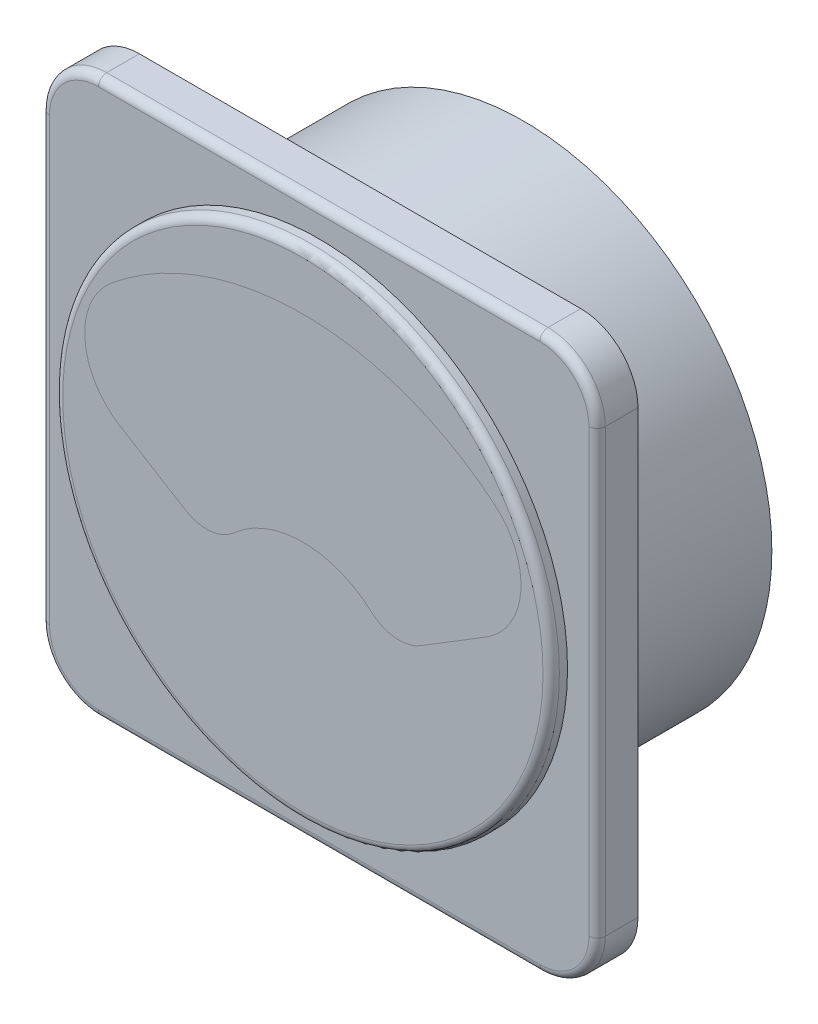
SolidWorks part; units mm, degrees
ref_plane "Front Plane" through (0, 0, 0) normal (0, 0, 1) x (1, 0, 0)
ref_plane "Top Plane" through (0, 0, 0) normal (0, 1, 0) x (1, 0, 0)
ref_plane "Right Plane" through (0, 0, 0) normal (1, 0, 0) x (0, 0, -1)
sketch "Sketch1" plane through (0, 0, 0) normal (0, 0, 1) x (1, 0, 0)
  circle A0 centre (0, 0) radius 30.3826
extrude "Boss-Extrude1" add sketch "Sketch1" against normal blind 20
sketch "Sketch2" plane through (0, 0, 0) normal (0, 0, 1) x (1, 0, 0)
  line L1 (-27, -34) -> (27, -34)
  line L2 (-34, -27) -> (-34, 27)
  line L3 (-27, 34) -> (27, 34)
  line L4 (34, -27) -> (34, 27)
  line L5 (-34, -34) -> (34, 34) construction
  line L6 (-34, 34) -> (34, -34) construction
  arc A0 (-34, 27) -> (-27, 34) centre (-27, 27) cw
  circle A1 centre (0, 0) radius 27.5
  arc A3 (-27, -34) -> (-34, -27) centre (-27, -27) cw
  arc A4 (27, -34) -> (34, -27) centre (27, -27) ccw
  arc A5 (34, 27) -> (27, 34) centre (27, 27) ccw
  dimension "D1" = 55
  dimension "D2" = 7
  dimension "D3" = 68
  dimension "D4" = 68
extrude "Boss-Extrude2" add sketch "Sketch2" along normal blind 5 separate body
sketch "Sketch3" plane through (0, 0, 5) normal (0, 0, 1) x (1, 0, 0)
  line L0 (14.3909, -4.5184) -> (22.3947, 0.3925)
  line L1 (0, 23.4246) -> (0, -13.3482) construction
  line L2 (-14.3909, -4.5184) -> (-22.3947, 0.3925)
  circle A0 centre (0, 0) radius 30.3826
  arc A1 (8.4322, -3.974) -> (-8.4322, -3.974) centre (0, -13.3482) ccw
  arc A2 (23.4198, 15.0023) -> (-23.4198, 15.0023) centre (0, -13.3482) ccw
  arc A3 (22.3947, 0.3925) -> (23.4198, 15.0023) centre (17.6879, 8.0636) ccw
  arc A4 (-22.3947, 0.3925) -> (-23.4198, 15.0023) centre (-17.6879, 8.0636) cw
  arc A5 (14.3909, -4.5184) -> (8.4322, -3.974) centre (11.776, -0.2567) cw
  arc A6 (-14.3909, -4.5184) -> (-8.4322, -3.974) centre (-11.776, -0.2567) ccw
  point P11 (31.3432, 5.883)
  point P14 (-31.3432, 5.883)
  dimension "D1" = 9
  dimension "D2" = 5
extrude "Boss-Extrude3" add sketch "Sketch3" along normal blind 2 separate body
sketch "Sketch4" plane through (0, 0, 0) normal (0, 0, 1) x (1, 0, 0)
  line L0 (-0.2927, -13.1129) -> (6.9482, 19.2105) construction
  line L1 (1.3143, -6.8541) -> (7.1433, 19.1668)
  line L2 (0.9239, -6.7667) -> (6.753, 19.2542)
  line L4 (-0.0976, -13.1566) -> (7.1433, 19.1668) construction
  line L5 (-0.4879, -13.0691) -> (6.753, 19.2542) construction
  arc A0 (0.9239, -6.7667) -> (1.3143, -6.8541) centre (-0.2927, -13.1129) ccw
  arc A2 (7.1433, 19.1668) -> (6.753, 19.2542) centre (6.9482, 19.2105) ccw
  dimension "D1" = 0.2
  dimension "D2" = 0.2
extrude "Boss-Extrude4" add sketch "Sketch4" along normal blind 1 separate body
sketch "Sketch5" plane through (0, 0, 7) normal (0, 0, 1) x (1, 0, 0)
  line L0 (14.3909, -4.5184) -> (22.3947, 0.3925)
  line L1 (-14.3909, -4.5184) -> (-22.3947, 0.3925)
  arc A0 (8.4322, -3.974) -> (-8.4322, -3.974) centre (0, -13.3482) ccw
  arc A1 (23.4198, 15.0023) -> (-23.4198, 15.0023) centre (0, -13.3482) ccw
  arc A2 (8.4322, -3.974) -> (14.3909, -4.5184) centre (11.776, -0.2567) ccw
  arc A3 (-8.4322, -3.974) -> (-14.3909, -4.5184) centre (-11.776, -0.2567) cw
  arc A4 (22.3947, 0.3925) -> (23.4198, 15.0023) centre (17.6879, 8.0636) ccw
  arc A5 (-22.3947, 0.3925) -> (-23.4198, 15.0023) centre (-17.6879, 8.0636) cw
  point P15 (31.3432, 5.883)
  point P18 (-31.3432, 5.883)
  dimension "D1" = 5
  dimension "D2" = 9
extrude "Boss-Extrude5" add sketch "Sketch5" against normal blind 1 separate body
fillet "Fillet1" radius 1 1 edges at (30.3826, 0, 7)
fillet "Fillet2" radius 1 8 edges at (-34, 0, 5) (-31.9497, 31.9497, 5) (0, 34, 5) (31.9497, 31.9497, 5) (34, 0, 5) (31.9497, -31.9497, 5) (0, -34, 5) (-31.9497, -31.9497, 5)
